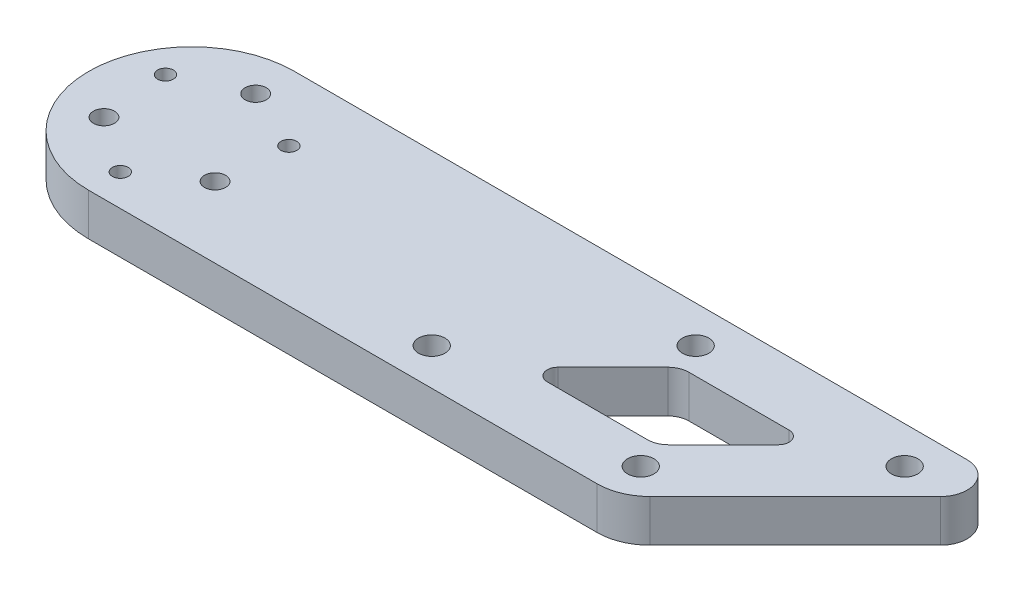
SolidWorks part; units mm, degrees
ref_plane "前视基准面" through (0, 0, 0) normal (0, 0, 1) x (1, 0, 0)
ref_plane "上视基准面" through (0, 0, 0) normal (0, 1, 0) x (1, 0, 0)
ref_plane "右视基准面" through (0, 0, 0) normal (1, 0, 0) x (0, 0, -1)
sketch "草图1" plane through (0, 0, 0) normal (0, 1, 0) x (1, 0, 0)
  line L0 (0, 19.5) -> (127.4289, 19.5)
  line L1 (0, 12.15) -> (-10.5222, -6.075) construction
  line L2 (-10.5222, -6.075) -> (10.5222, -6.075) construction
  line L3 (10.5222, -6.075) -> (0, 12.15) construction
  line L4 (-11.6913, 6.75) -> (0, -13.5) construction
  line L5 (0, -13.5) -> (11.6913, 6.75) construction
  line L6 (11.6913, 6.75) -> (-11.6913, 6.75) construction
  line L7 (0, -19.5) -> (96.3579, -19.5)
  line L8 (103.4289, -16.5711) -> (130.9645, 10.9645)
  line L9 (0, 0) -> (120, 0) construction
  circle A0 centre (0, 0) radius 19.5 construction
  circle A1 centre (0, 0) radius 13.5 construction
  circle A2 centre (0, 0) radius 12.15 construction
  circle A3 centre (0, 0) radius 6.075 construction
  circle A4 centre (0, 0) radius 6.75 construction
  circle A5 centre (0, 12.15) radius 2
  circle A6 centre (-10.5222, -6.075) radius 2
  circle A7 centre (10.5222, -6.075) radius 2
  circle A8 centre (-11.6913, 6.75) radius 1.5
  circle A9 centre (11.6913, 6.75) radius 1.5
  circle A10 centre (0, -13.5) radius 1.5
  arc A11 (0, 19.5) -> (0, -19.5) centre (0, 0) ccw
  arc A12 (96.3579, -19.5) -> (103.4289, -16.5711) centre (96.3579, -9.5) ccw
  arc A13 (127.4289, 19.5) -> (130.9645, 10.9645) centre (127.4289, 14.5) cw
  dimension "D1" = 27
  dimension "D2" = 24.3
  dimension "D3" = 4
  dimension "D4" = 3
  dimension "D5" = 39
  dimension "D7" = 10
  dimension "D8" = 5
  dimension "D6" = 135
  dimension "D9" = 120
extrude "凸台-拉伸1" add sketch "草图1" along normal blind 8
sketch "草图2" plane through (0, 0, 0) normal (0, -1, 0) x (1, 0, 0)
  line L0 (93.8726, 7.5) -> (74.902, 7.5)
  line L1 (105.701, -7.5) -> (86.7304, -7.5)
  line L2 (73.4878, 4.0858) -> (83.902, -6.3284)
  line L3 (96.701, 6.3284) -> (107.1152, -4.0858)
  arc A0 (93.8726, 7.5) -> (96.701, 6.3284) centre (93.8726, 3.5) cw
  arc A1 (107.1152, -4.0858) -> (105.701, -7.5) centre (105.701, -5.5) cw
  arc A2 (86.7304, -7.5) -> (83.902, -6.3284) centre (86.7304, -3.5) cw
  arc A3 (74.902, 7.5) -> (73.4878, 4.0858) centre (74.902, 5.5) ccw
  arc A4 (83.902, -6.3284) -> (86.7304, -7.5) centre (86.7304, -3.5) ccw construction
extrude "切除-拉伸1" cut sketch "草图2" against normal through all
sketch "草图3" plane through (0, 0, 0) normal (0, -1, 0) x (1, 0, 0)
  circle A0 centre (97.6005, 12.5) radius 2.5
  circle A1 centre (122.6005, -12.5) radius 2.5
  circle A2 centre (83.0025, -12.5) radius 2.5
  circle A3 centre (58.0025, 12.5) radius 2.5
extrude "切除-拉伸2" cut sketch "草图3" against normal through all both and the other way through all
